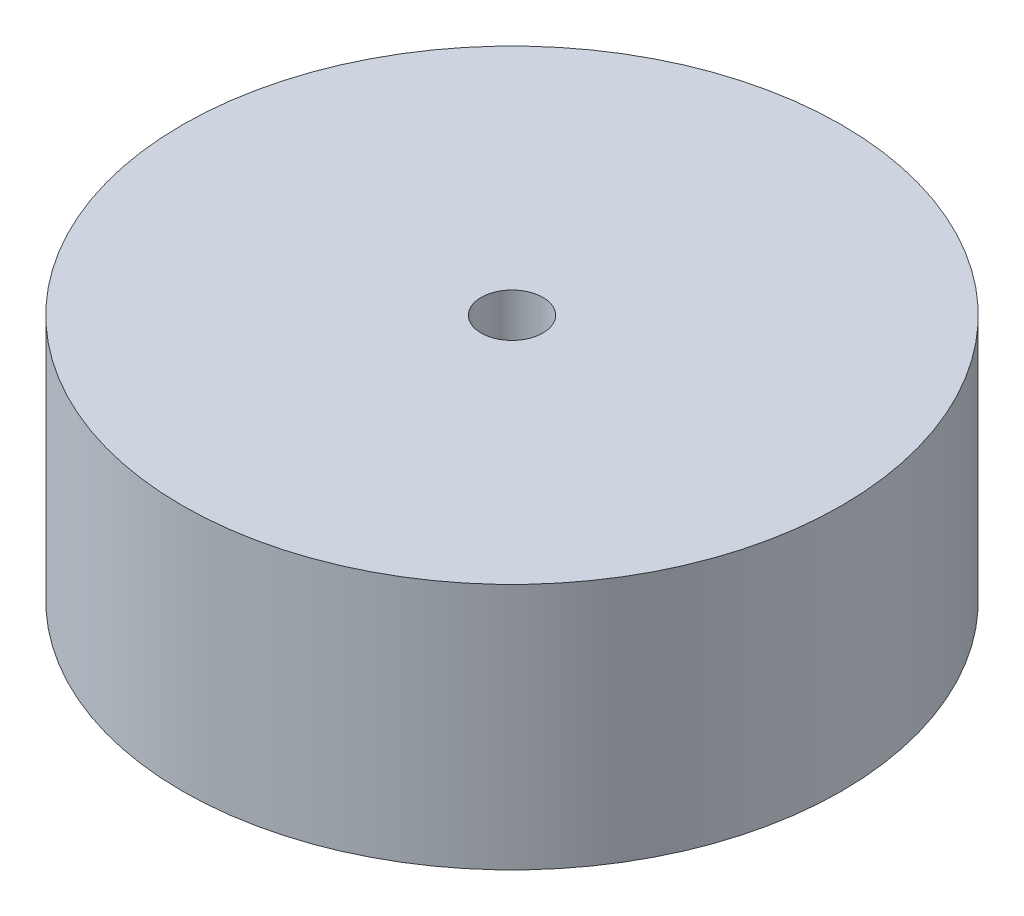
SolidWorks part; units mm, degrees
ref_plane "Front Plane" through (0, 0, 0) normal (0, 0, 1) x (1, 0, 0)
ref_plane "Top Plane" through (0, 0, 0) normal (0, 1, 0) x (1, 0, 0)
ref_plane "Right Plane" through (0, 0, 0) normal (1, 0, 0) x (0, 0, -1)
sketch "Sketch1" plane through (0, 0, 0) normal (0, 1, 0) x (1, 0, 0)
  circle A0 centre (0, 0) radius 32
  dimension "D1" = 64
extrude "Boss-Extrude1" add sketch "Sketch1" along normal blind 24 contours A0
sketch "Sketch2" plane through (0, 24, 0) normal (0, 1, 0) x (1, 0, 0)
  circle A0 centre (0, 0) radius 3
  dimension "D1" = 6
extrude "Cut-Extrude1" cut sketch "Sketch2" against normal blind 24
equation "\"MDFThickness\"= .2in"
equation "\"D1@Boss-Extrude1\"= \"WheelThickness\""
equation "\"D1@Cut-Extrude1\"=\"WheelThickness\""
equation "\"WheelThickness\"= 24mm"
